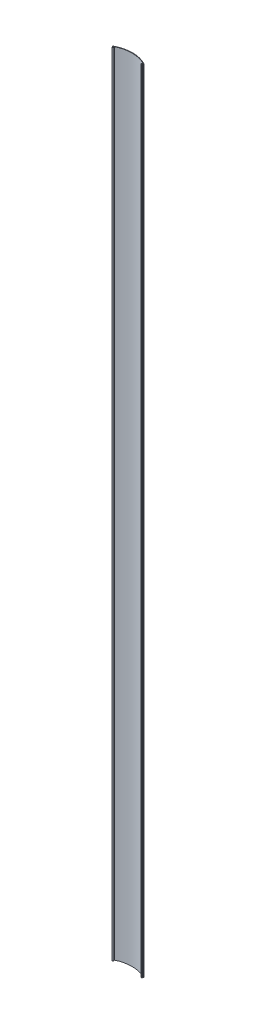
SolidWorks part; units mm, degrees
material "6463-T6"
ref_plane "Front Plane" through (0, 0, 0) normal (0, 0, 1) x (1, 0, 0)
ref_plane "Top Plane" through (0, 0, 0) normal (0, 1, 0) x (1, 0, 0)
ref_plane "Right Plane" through (0, 0, 0) normal (1, 0, 0) x (0, 0, -1)
sketch "Sketch1" plane through (0, 0, 0) normal (0, 1, 0) x (1, 0, 0)
  line L0 (0, 6.3541) -> (101.5848, 6.3541) construction
  line L1 (0, 0) -> (101.5848, 0) construction
  line L2 (0, 0) -> (0, 25.4) construction
  line L3 (0, 25.4) -> (101.5848, 25.4) construction
  line L4 (101.5848, 0) -> (101.5848, 25.4) construction
  line L5 (0, 12.7) -> (101.5848, 12.7) construction
  line L6 (0, 19.05) -> (101.5848, 19.05) construction
  line L7 (50.7924, 25.4) -> (50.7924, 0) construction
  line L8 (12.7, 25.4) -> (12.7, 0) construction
  line L9 (76.1924, 25.4) -> (76.1924, 0) construction
  line L10 (25.4, 25.4) -> (25.4, 0) construction
  line L11 (38.1, 25.4) -> (38.1, 0) construction
  line L12 (63.4924, 25.4) -> (63.4924, 0) construction
  line L13 (88.8924, 25.4) -> (88.8924, 0) construction
  line L15 (101.5848, 6.3541) -> (101.5848, 4.3221)
  line L16 (100.0608, 5.4351) -> (100.0608, 4.3221)
  line L17 (100.5688, 3.8141) -> (101.0768, 3.8141)
  line L19 (0, 0) -> (-3.2676, 0) construction
  line L20 (1.3386, 5.3381) -> (0, 5.3381)
  line L26 (90.0621, 10.016) -> (95.6249, 0.381)
  line L27 (95.6249, 0.381) -> (95.6249, 0)
  line L28 (95.6249, 0) -> (97.1489, 0)
  line L29 (97.1489, 0) -> (97.1489, 0.381)
  line L30 (97.1489, 0.381) -> (112.7608, 0.381)
  line L31 (112.7608, 0.381) -> (112.7608, 0)
  line L32 (112.7608, 0) -> (114.2848, 0)
  line L33 (114.2848, 0) -> (114.2848, 1.905)
  line L34 (114.2848, 1.905) -> (96.5048, 1.905)
  line L35 (96.5048, 1.905) -> (92.3687, 9.0689)
  line L36 (97.1489, 0.381) -> (95.6249, 0.381) construction
  line L38 (0, 5.3381) -> (0, 6.3541)
  line L39 (101.5848, 5.3381) -> (100.8228, 3.8141)
  arc A0 (101.5848, 6.3541) -> (0, 6.3541) centre (50.7924, -88.9) ccw
  arc A1 (100.0608, 5.4351) -> (1.3386, 5.3381) centre (50.7924, -88.9) ccw
  circle A2 centre (50.7924, -88.9) radius 107.95 construction
  circle A3 centre (50.7924, -88.9) radius 106.426 construction
  arc A4 (100.0608, 4.3221) -> (100.5688, 3.8141) centre (100.5688, 4.3221) ccw
  arc A5 (101.0768, 3.8141) -> (101.5848, 4.3221) centre (101.0768, 4.3221) ccw
  point P33 (100.0608, 3.8141)
  point P38 (101.5848, 3.8141)
  dimension "D12" = 2.54
  dimension "D14" = 0.508
  dimension "D16" = 107.95
  dimension "D1" = 101.5848
  dimension "D2" = 25.4
  dimension "D3" = 12.7
  dimension "D4" = 12.7
  dimension "D5" = 12.7
  dimension "D6" = 12.7
  dimension "D7" = 12.7
  dimension "D8" = 12.7
  dimension "D9" = 1.016
  dimension "D10" = 6.35
  dimension "D13" = 1.524
  dimension "D15" = 1.016
  dimension "D20" = 0.762
  dimension "D21" = 1.524
  dimension "D22" = 1.524
  dimension "D23" = 1.524
  dimension "D24" = 12.7
  dimension "D25" = 5.08
  dimension "D26" = 60
  dimension "D27" = 1.524
  dimension "D11" = 1.524
extrude "Boss-Extrude1" add sketch "Sketch1" along normal blind 2590.8
sketch "Sketch3" plane through (0, 2590.8, 0) normal (0, 1, 0) x (1, 0, 0)
  line L1 (101.5848, 6.3541) -> (101.5848, 5.3381) construction
  line L2 (100.0608, 2.9237) -> (101.5848, 2.9237)
  line L3 (101.5848, 2.9237) -> (101.5848, 5.5921)
  line L4 (101.5848, 5.5921) -> (100.0608, 5.4351)
  line L5 (100.0608, 5.4351) -> (100.0608, 2.9237)
  line L6 (0, 5.5921) -> (0.4068, 4.4744)
  line L7 (0, 5.3381) -> (0, 6.3541) construction
  line L8 (0.4068, 4.4744) -> (0, 4.4744)
  line L9 (0, 4.4744) -> (0, 5.5921)
  dimension "D1" = 0.762
  dimension "D2" = 0.762
  dimension "D3" = 2.6684
  dimension "D4" = 20
  dimension "D5" = 1.1176
extrude "Cut-Extrude1" cut sketch "Sketch3" against normal through all
sketch "Sketch2" plane through (0, 2590.8, 0) normal (0, 1, 0) x (1, 0, 0)
  line L0 (101.5848, 5.5921) -> (97.7112, 6.6255)
  line L1 (101.5848, 6.3541) -> (101.5848, 5.5921) construction
  line L2 (101.2381, 4.6396) -> (101.5848, 5.5921)
  line L3 (101.2381, 4.6396) -> (98.7908, 4.6396)
  line L4 (98.7908, 2.2266) -> (99.8157, 2.2266)
  line L5 (100.1737, 1.7153) -> (99.9473, 1.0931)
  line L7 (101.5848, 6.3541) -> (101.5848, 5.5921) construction
  line L9 (50.7924, -88.9) -> (50.7924, 34.1205) construction
  line L10 (1.411, 1.7153) -> (1.6375, 1.0931)
  line L15 (2.794, 2.2266) -> (1.7691, 2.2266)
  line L19 (0.3467, 4.6396) -> (2.794, 4.6396)
  line L20 (0.3467, 4.6396) -> (0, 5.5921)
  line L21 (0, 5.5921) -> (3.8736, 6.6255)
  arc A1 (3.8888, 5.9345) -> (3.8736, 6.6255) centre (4.0415, 6.2835) cw
  arc A2 (98.7908, 2.2266) -> (98.7908, 4.6396) centre (98.7908, 3.4331) cw
  arc A3 (99.7187, 0.8651) -> (97.696, 5.9345) centre (98.7908, 3.4331) cw
  arc A4 (99.8157, 2.2266) -> (100.1737, 1.7153) centre (99.8157, 1.8456) cw
  arc A5 (99.9473, 1.0931) -> (99.7187, 0.8651) centre (99.5892, 1.2234) cw
  arc A12 (97.696, 5.9345) -> (97.7112, 6.6255) centre (97.5432, 6.2835) ccw
  arc A13 (1.6375, 1.0931) -> (1.866, 0.8651) centre (1.9955, 1.2234) ccw
  arc A14 (1.7691, 2.2266) -> (1.411, 1.7153) centre (1.7691, 1.8456) ccw
  arc A15 (1.866, 0.8651) -> (3.8888, 5.9345) centre (2.794, 3.4331) ccw
  arc A16 (2.794, 2.2266) -> (2.794, 4.6396) centre (2.794, 3.4331) ccw
  arc A17 (100.0608, 5.4351) -> (1.3386, 5.3381) centre (50.7924, -88.9) ccw construction
  dimension "D2" = 2.413
  dimension "D3" = 5.461
  dimension "D4" = 0.381
  dimension "D14" = 0.762
  dimension "D12" = 20
  dimension "D6" = 2.794
  dimension "D5" = 0.9525
  dimension "D15" = 0.762
extrude "Boss-Extrude2" add sketch "Sketch2" against normal up to surface (2590.8 mm away) up to face at (43.5213, 0, -9.2627)
fillet "Fillet1" radius 0.508 2 edges at (101.2381, 1295.4, -4.6396) (0.3467, 1295.4, -4.6396)
